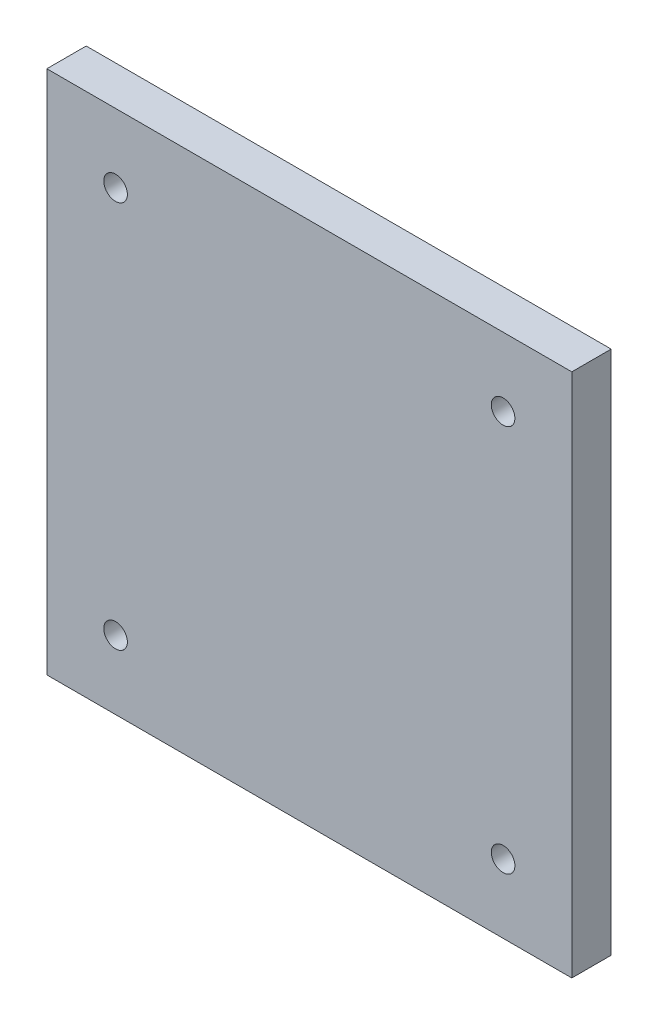
SolidWorks part; units mm, degrees
ref_plane "Front Plane" through (0, 0, 0) normal (0, 0, 1) x (1, 0, 0)
ref_plane "Top Plane" through (0, 0, 0) normal (0, 1, 0) x (1, 0, 0)
ref_plane "Right Plane" through (0, 0, 0) normal (1, 0, 0) x (0, 0, -1)
sketch "Sketch1" plane through (0, 0, 0) normal (0, 0, 1) x (1, 0, 0)
  line L0 (0, 0) -> (0, 50.8) construction
  line L1 (-50.8, 50.8) -> (50.8, 50.8)
  line L2 (-50.8, 50.8) -> (-50.8, -50.8)
  line L3 (-50.8, -50.8) -> (50.8, -50.8)
  line L4 (50.8, 50.8) -> (50.8, -50.8)
  line L5 (-50.8, 50.8) -> (50.8, -50.8) construction
  line L6 (-50.8, -50.8) -> (50.8, 50.8) construction
  line L7 (0, 50.8) -> (0, 0) construction
  line L8 (0, 0) -> (50.8, 0) construction
  line L9 (50.8, 0) -> (-50.8, 0) construction
  line L10 (-50.8, 0) -> (0, 0) construction
  line L11 (0, 0) -> (0, -50.8) construction
  circle A0 centre (-37.5001, 37.5001) radius 2.286
  circle A1 centre (37.5001, 37.5001) radius 2.286
  circle A2 centre (37.5001, -37.5001) radius 2.286
  circle A3 centre (-37.5001, -37.5001) radius 2.286
  point P0 (0, 0)
  dimension "D3" = 4.572
  dimension "D1" = 101.6
  dimension "D2" = 101.6
  dimension "D4" = 37.5001
  dimension "D5" = 37.5001
  dimension "D6" = 37.5001
  dimension "D7" = 37.5001
  dimension "D8" = 37.5001
  dimension "D9" = 37.5001
  dimension "D10" = 37.5001
  dimension "D11" = 37.5001
extrude "Boss-Extrude1" add sketch "Sketch1" along normal blind 7.62
